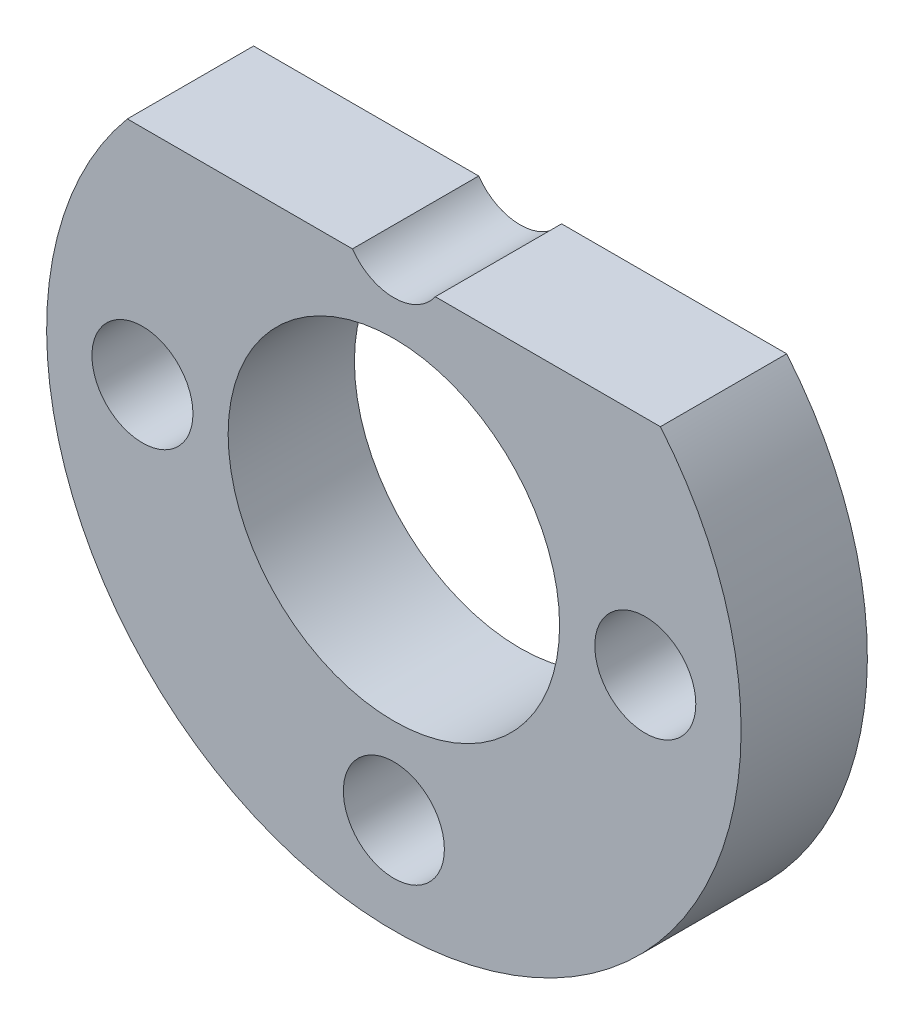
SolidWorks part; units mm, degrees
material "Thornel Mat VMA"
ref_plane "Plano frontal" through (0, 0, 0) normal (0, 0, 1) x (1, 0, 0)
ref_plane "Plano superior" through (0, 0, 0) normal (0, 1, 0) x (1, 0, 0)
ref_plane "Plano direito" through (0, 0, 0) normal (1, 0, 0) x (0, 0, -1)
sketch "Esboço1" plane through (0, 0, 0) normal (0, 0, 1) x (1, 0, 0)
  line L0 (95.2028, -295.7159) -> (112.0904, -295.7159)
  circle A0 centre (103.6466, -302.7659) radius 7.9647 construction
  arc A1 (95.2028, -295.7159) -> (112.0904, -295.7159) centre (103.6466, -302.7659) ccw
  dimension "D1" = 11
extrude "Ressalto-extrusão1" add sketch "Esboço1" along normal blind 4
sketch "Esboço2" plane through (0, 0, 4) normal (0, 0, 1) x (1, 0, 0)
  circle A0 centre (103.6466, -302.7659) radius 5.25
  dimension "10.5" = 10.5
extrude "Corte-extrusão1" cut sketch "Esboço2" against normal blind 4
hole_wizard "M3 Clearance Hole1" positions "Sketch3" profile "Sketch2" hole size "M3" standard "ISO" end condition through all
sketch "Sketch3" plane through (0, 0, 4) normal (0, 0, 1) x (1, 0, 0)
  circle A0 centre (103.6466, -302.7659) radius 7.9647
  point P4 (95.6819, -302.7659)
  point P6 (111.6113, -302.7659)
  point P8 (103.6466, -310.7307)
  point P10 (103.6466, -294.8012)
sketch "Sketch2" plane through (95.6819, -302.7659, 4) normal (1, 0, 0) x (0, -1, 0)
  line L0 (0, 0) -> (0, 4)
  line L1 (0, 4) -> (1.6, 4)
  line L2 (1.6, 4) -> (1.6, 0)
  line L5 (1.6, 0) -> (0, 0)
  line L11 (0, -6.35) -> (0, 107.95) construction
  dimension "Thru Hole Dia." = 3.2
  dimension "Thru Hole Depth" = 4
